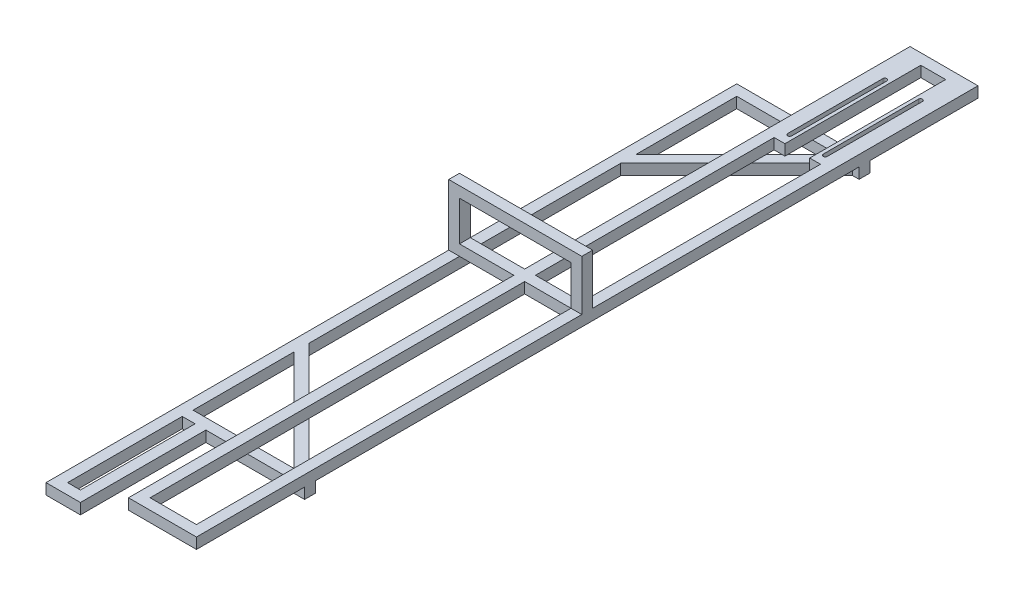
SolidWorks part; units mm, degrees
ref_plane "Front Plane" through (0, 0, 0) normal (0, 0, 1) x (1, 0, 0)
ref_plane "Top Plane" through (0, 0, 0) normal (0, 1, 0) x (1, 0, 0)
ref_plane "Right Plane" through (0, 0, 0) normal (1, 0, 0) x (0, 0, -1)
sketch "Sketch1" plane through (0, 0, 0) normal (0, 1, 0) x (1, 0, 0)
  line L1 (-50, 575) -> (50, 575)
  line L2 (-50, 575) -> (-50, -575)
  line L3 (-50, -575) -> (50, -575)
  line L4 (50, 575) -> (50, -575)
  line L8 (-34.125, 559.125) -> (34.125, 559.125)
  line L9 (34.125, 559.125) -> (34.125, -559.125)
  line L10 (-34.125, -559.125) -> (34.125, -559.125)
  line L11 (-34.125, 559.125) -> (-34.125, -559.125)
  point P4 (0, 575)
  point P6 (50, 0)
  dimension "D1" = 100
  dimension "D2" = 1150
  dimension "D3" = 15.875
extrude "Boss-Extrude1" add sketch "Sketch1" along normal blind 15.875
sketch "Sketch3" plane through (0, 15.875, 0) normal (0, 1, 0) x (1, 0, 0)
  line L0 (-145.875, 558.625) -> (-145.875, -591.375) construction
  line L3 (34.125, 400) -> (-130, 400)
  line L4 (-130, 220.5939) -> (-130, 400)
  line L6 (50, 415.875) -> (-145.875, 415.875)
  line L7 (-145.875, 217.7568) -> (-145.875, 415.875)
  line L9 (50, 400) -> (50, 415.875)
  line L10 (-8.7312, 0) -> (8.7312, 0) construction
  line L11 (50, -400) -> (50, -415.875)
  line L13 (-145.875, 217.7568) -> (-145.875, -415.875)
  line L14 (50, -415.875) -> (-145.875, -415.875)
  line L15 (-130, 220.5939) -> (-130, -400)
  line L18 (34.125, -400) -> (-130, -400)
  line L19 (50, -575) -> (50, 575) construction
  line L20 (50, -312.7388) -> (-145.875, 217.7568) construction
  line L21 (34.125, -223.912) -> (-130, 220.5939) construction
  line L22 (34.125, 400) -> (50, 400)
  line L23 (34.125, -400) -> (50, -400)
  line L25 (50, -312.7388) -> (50, 415.875) construction
  line L26 (34.125, -223.912) -> (34.125, 400) construction
  dimension "D1" = 400
  dimension "D3" = 15.875
extrude "Boss-Extrude2" add sketch "Sketch3" against normal blind 15.875 from surface at -15.875 starting at face at (0, 0, 0)
sketch "Sketch5" plane through (0, 0, 0) normal (0, 0, 1) x (1, 0, 0)
  line L0 (-145.875, 955.91) -> (-145.875, -19.875) construction
  line L1 (50, 0) -> (-145.875, 0)
  line L2 (50, 0) -> (50, 90)
  line L3 (50, 90) -> (-145.875, 90)
  line L4 (-145.875, 0) -> (-145.875, 90)
  line L5 (34.125, 74.125) -> (-130, 74.125)
  line L6 (-130, 15.875) -> (-130, 74.125)
  line L7 (34.125, 15.875) -> (-130, 15.875)
  line L8 (34.125, 15.875) -> (34.125, 74.125)
  dimension "D1" = 90
  dimension "D2" = 15.875
extrude "Boss-Extrude3" add sketch "Sketch5" along normal mid plane 15.875
sketch "Sketch6" plane through (0, 0, 0) normal (0, -1, 0) x (1, 0, 0)
  line L6 (-34.125, -559.125) -> (-18.25, -559.125)
  line L7 (-34.125, -559.125) -> (-34.125, -359.125)
  line L8 (-34.125, -359.125) -> (-18.25, -359.125)
  line L9 (-18.25, -559.125) -> (-18.25, -359.125)
  line L10 (34.125, -559.125) -> (18.25, -559.125)
  line L11 (34.125, -559.125) -> (34.125, -359.125)
  line L12 (34.125, -359.125) -> (18.25, -359.125)
  line L13 (18.25, -559.125) -> (18.25, -359.125)
  line L14 (34.125, -559.125) -> (-34.125, -559.125) construction
  dimension "D1" = 15.875
  dimension "D2" = 15.875
  dimension "D4" = 200
extrude "Boss-Extrude4" add sketch "Sketch6" against normal blind 15.875
sketch "Sketch7" plane through (0, 0, 0) normal (0, -1, 0) x (1, 0, 0)
  line L0 (-26.1875, -374.125) -> (-26.1875, -514.125) construction
  line L1 (-23.1875, -374.125) -> (-23.1875, -514.125)
  line L2 (-29.1875, -374.125) -> (-29.1875, -514.125)
  line L3 (26.1875, -374.125) -> (26.1875, -514.125) construction
  line L4 (29.1875, -374.125) -> (29.1875, -514.125)
  line L5 (23.1875, -374.125) -> (23.1875, -514.125)
  line L6 (-18.25, -359.125) -> (-34.125, -359.125) construction
  line L7 (34.125, -359.125) -> (18.25, -359.125) construction
  arc A0 (-23.1875, -374.125) -> (-29.1875, -374.125) centre (-26.1875, -374.125) ccw
  arc A1 (-29.1875, -514.125) -> (-23.1875, -514.125) centre (-26.1875, -514.125) ccw
  arc A2 (29.1875, -374.125) -> (23.1875, -374.125) centre (26.1875, -374.125) ccw
  arc A3 (23.1875, -514.125) -> (29.1875, -514.125) centre (26.1875, -514.125) ccw
  point P2 (-26.1875, -444.125)
  point P7 (26.1875, -444.125)
  point P17 (-26.1875, -359.125)
  point P20 (26.1875, -359.125)
  dimension "D1" = 3
  dimension "D2" = 140
  dimension "D3" = 15
extrude "Cut-Extrude1" cut sketch "Sketch7" against normal blind 15.875
sketch "Sketch8" plane through (0, 0, 0) normal (0, 1, 0) x (1, 0, 0)
  line L1 (-95.25, -600.5) -> (-145.875, -600.5)
  line L2 (-95.25, -600.5) -> (-95.25, -400)
  line L3 (-95.25, -400) -> (-145.875, -400)
  line L4 (-145.875, -600.5) -> (-145.875, -400)
  line L5 (-130, -400) -> (-50, -400) construction
  line L6 (-111.125, -415.875) -> (-130, -415.875)
  line L7 (-130, -584.625) -> (-130, -415.875)
  line L8 (-111.125, -584.625) -> (-130, -584.625)
  line L9 (-111.125, -584.625) -> (-111.125, -415.875)
  line L10 (-145.875, -7.9375) -> (-145.875, -415.875) construction
  line L12 (-130, -590.5) -> (-145.875, -590.5) construction
  point P5 (-145.875, -400)
  point P7 (-97.9375, -400)
  point P17 (-137.9375, -590.5)
  dimension "D2" = 10
  dimension "D3" = 50.625
  dimension "D1" = 15.875
extrude "Boss-Extrude5" add sketch "Sketch8" against normal blind 15.875
sketch "Sketch9" plane through (0, 0, 0) normal (0, 1, 0) x (1, 0, 0)
  line L0 (45.3503, -404.6497) -> (34.125, -415.875)
  line L1 (45.3503, -404.6497) -> (-134.6497, -224.6497)
  line L2 (34.125, -415.875) -> (-145.875, -235.875)
  line L3 (-134.6497, -224.6497) -> (-145.875, -235.875)
  line L5 (34.125, -559.125) -> (34.125, -7.9375) construction
  line L6 (-34.125, -415.875) -> (34.125, -415.875) construction
  line L8 (-34.125, -400) -> (34.125, -400) construction
  line L10 (-145.875, 558.625) -> (-145.875, -591.375) construction
  point P10 (0, 0)
  point P11 (0, 0)
  point P12 (-199.6063, -199.5939)
  dimension "D1" = 15.875
  dimension "D2" = 45
extrude "Boss-Extrude6" add sketch "Sketch9" against normal blind 15.875
mirror "Mirror1" about plane through (0, 0, 0) normal (0, 0, 1) of "Boss-Extrude6"
